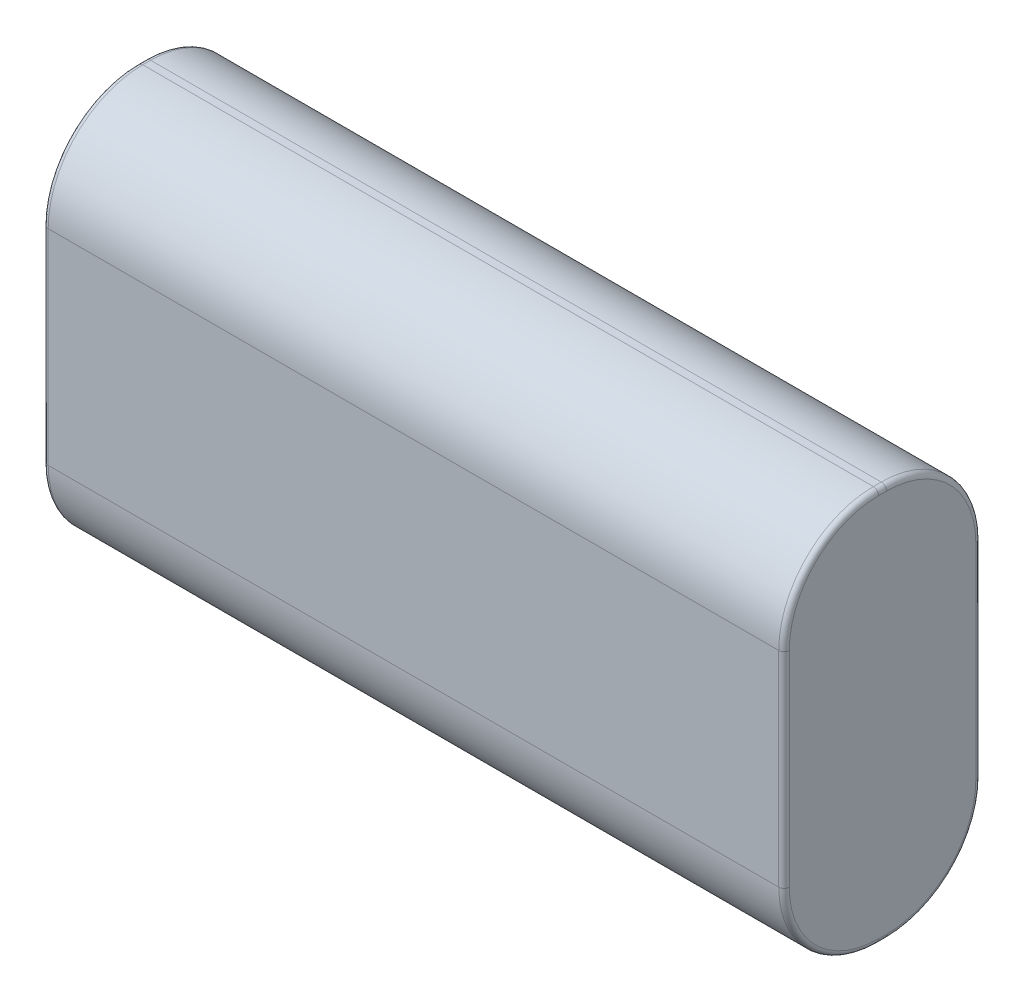
SolidWorks part; units mm, degrees
ref_plane "前视基准面" through (0, 0, 0) normal (0, 0, 1) x (1, 0, 0)
ref_plane "上视基准面" through (0, 0, 0) normal (0, 1, 0) x (1, 0, 0)
ref_plane "右视基准面" through (0, 0, 0) normal (1, 0, 0) x (0, 0, -1)
other "Configuration Table"
sketch "草图1" plane through (0, 0, 0) normal (1, 0, 0) x (0, 0, -1)
  line L0 (0, 0) -> (18.75, 0)
  line L1 (18.75, 0) -> (18.75, 37.5)
  line L2 (18.75, 37.5) -> (0, 37.5)
  line L3 (0, 37.5) -> (0, 0)
extrude "凸台-拉伸1" add sketch "草图1" along normal blind 70.5
fillet "圆角1" radius 9 4 edges at (35.25, 0, -18.75) (35.25, 0, 0) (35.25, 37.5, -18.75) (35.25, 37.5, 0)
fillet "圆角2" radius 0.5 16 edges at (0, 34.864, -16.114) (0, 37.5, -9.375) (0, 34.864, -2.636) (0, 18.75, 0) (0, 2.636, -2.636) (0, 0, -9.375) (0, 2.636, -16.114) (0, 18.75, -18.75) (70.5, 2.636, -2.636) (70.5, 18.75, 0) (70.5, 34.864, -2.636) (70.5, 37.5, -9.375) (70.5, 34.864, -16.114) (70.5, 18.75, -18.75) (70.5, 2.636, -16.114) (70.5, 0, -9.375)
